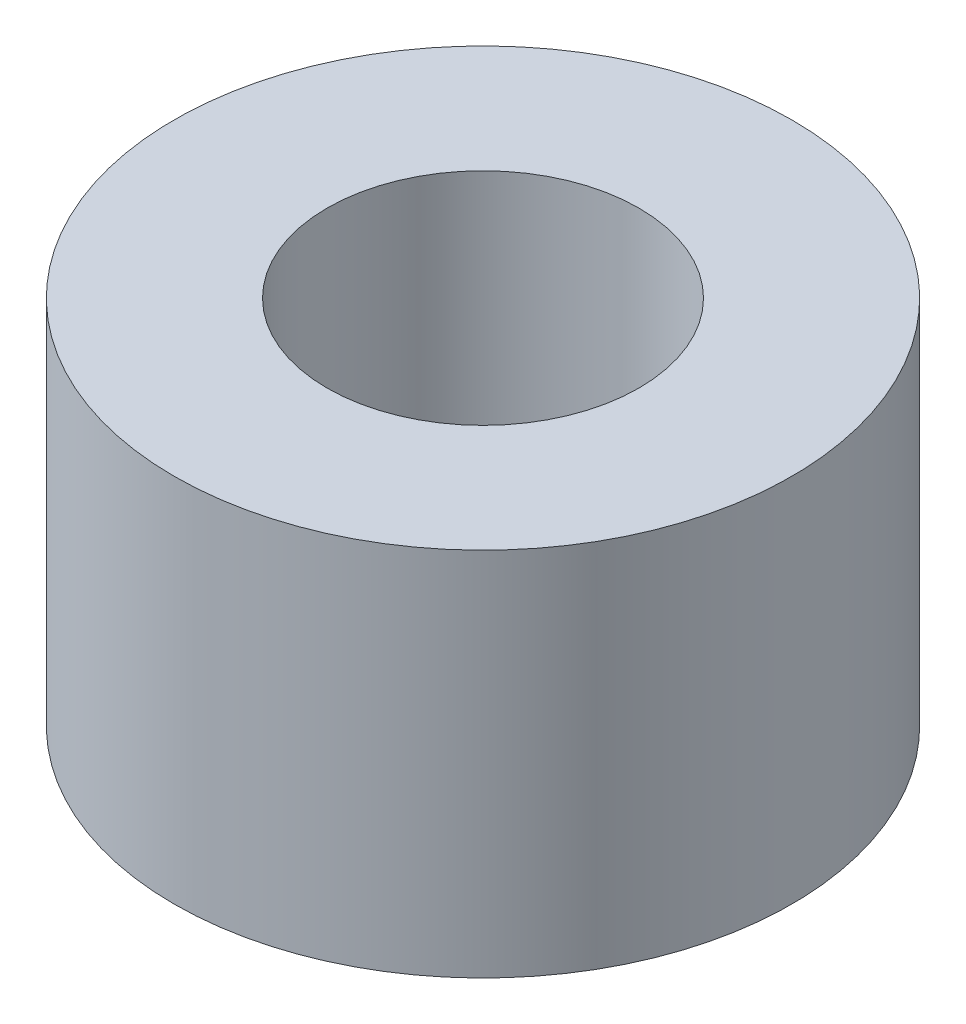
SolidWorks part; units mm, degrees
ref_plane "Front Plane" through (0, 0, 0) normal (0, 0, 1) x (1, 0, 0)
ref_plane "Top Plane" through (0, 0, 0) normal (0, 1, 0) x (1, 0, 0)
ref_plane "Right Plane" through (0, 0, 0) normal (1, 0, 0) x (0, 0, -1)
sketch "Sketch1" plane through (0, 0, 0) normal (0, 1, 0) x (1, 0, 0)
  circle A0 centre (0, 0) radius 5
  circle A1 centre (0, 0) radius 2.525
  dimension "D1" = 5.05
  dimension "D2" = 10
extrude "Boss-Extrude1" add sketch "Sketch1" along normal blind 6
